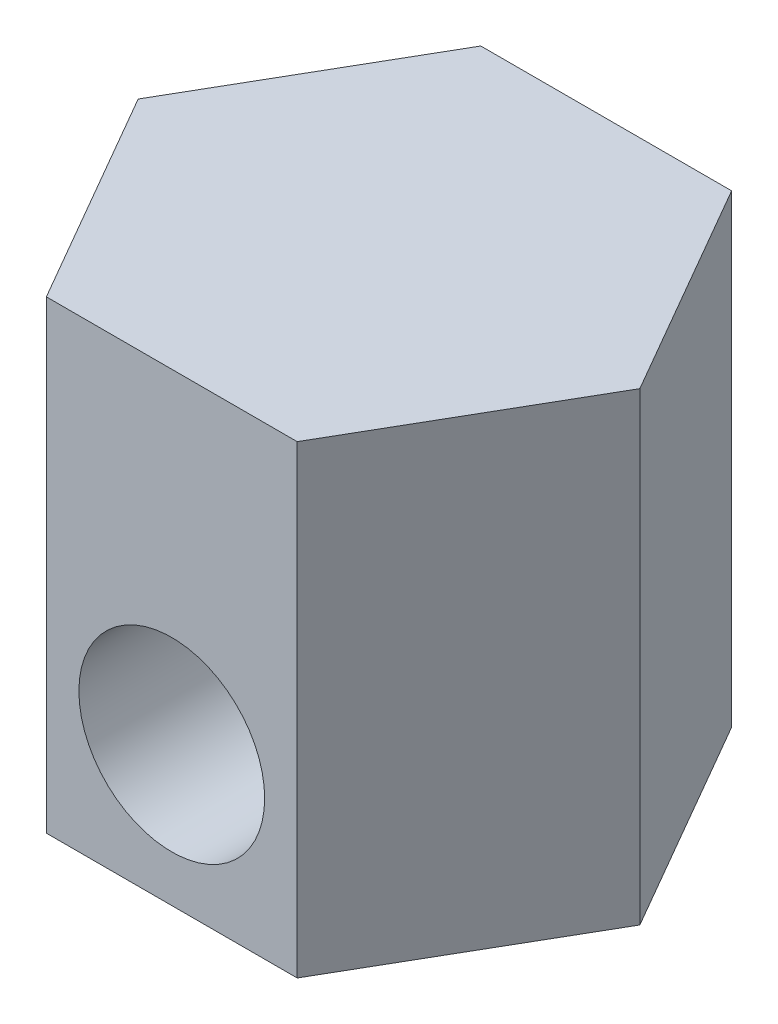
SolidWorks part; units mm, degrees
ref_plane "Alzado" through (0, 0, 0) normal (0, 0, 1) x (1, 0, 0)
ref_plane "Planta" through (0, 0, 0) normal (0, 1, 0) x (1, 0, 0)
ref_plane "Vista lateral" through (0, 0, 0) normal (1, 0, 0) x (0, 0, -1)
sketch "Croquis1" plane through (0, 0, 0) normal (0, 1, 0) x (1, 0, 0)
  line L1 (2.7, 0) -> (1.35, 2.3383)
  line L2 (1.35, 2.3383) -> (-1.35, 2.3383)
  line L3 (-1.35, 2.3383) -> (-2.7, 0)
  line L4 (-2.7, 0) -> (-1.35, -2.3383)
  line L5 (-1.35, -2.3383) -> (1.35, -2.3383)
  line L6 (1.35, -2.3383) -> (2.7, 0)
  circle A0 centre (0, 0) radius 2.3383 construction
  dimension "D1" = 2.7
extrude "Saliente-Extruir1" add sketch "Croquis1" along normal blind 5
sketch "Croquis2" plane through (0, 0, 2.3383) normal (0, 0, 1) x (1, 0, 0)
  line L0 (0, 0) -> (0, 1) construction
  line L1 (-1.35, 0) -> (1.35, 0) construction
  circle A0 centre (0, 1) radius 0.5
  dimension "D1" = 1
  dimension "D2" = 1
extrude "Cortar-Extruir1" cut sketch "Croquis2" against normal through all
sketch "Croquis3" plane through (0, 0, 2.3383) normal (0, 0, 1) x (1, 0, 0)
  line L0 (0, 0) -> (0, 1.5) construction
  line L1 (-1.35, 0) -> (1.35, 0) construction
  circle A0 centre (0, 1.5) radius 1
  dimension "D1" = 2
  dimension "D2" = 1.5
extrude "Cortar-Extruir2" cut sketch "Croquis3" against normal blind 2
